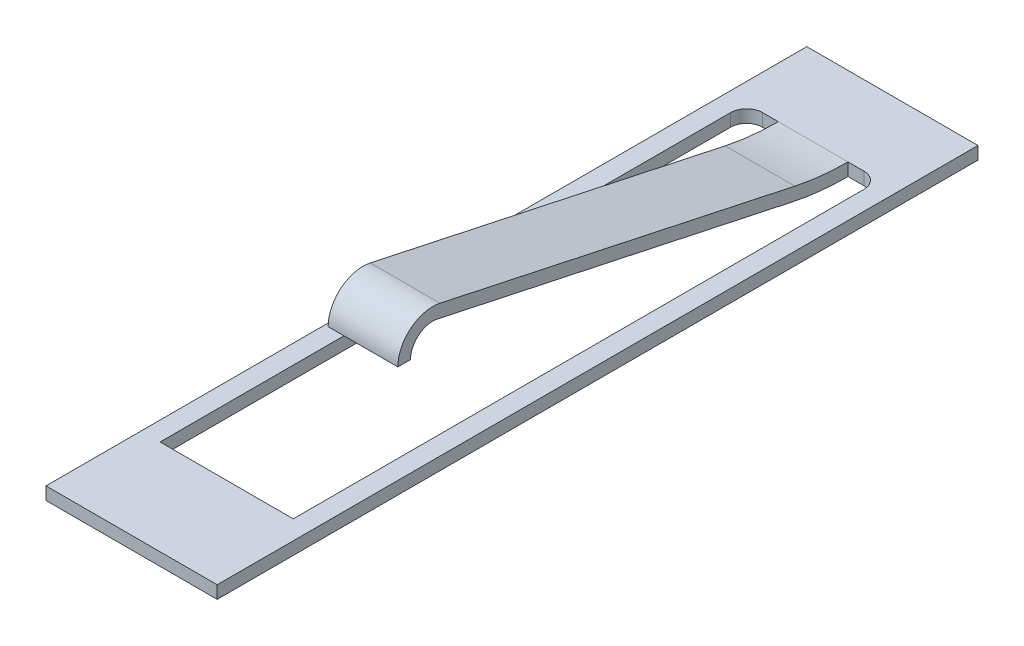
SolidWorks part; units mm, degrees
ref_plane "Front Plane" through (0, 0, 0) normal (0, 0, 1) x (1, 0, 0)
ref_plane "Top Plane" through (0, 0, 0) normal (0, 1, 0) x (1, 0, 0)
ref_plane "Right Plane" through (0, 0, 0) normal (1, 0, 0) x (0, 0, -1)
sketch "Sketch1" plane through (0, 0, 0) normal (0, 1, 0) x (1, 0, 0)
  line L0 (0, 6) -> (0, 0) construction
  line L1 (-1.35, 6) -> (1.35, 6)
  line L2 (-1.35, 6) -> (-1.35, -6)
  line L3 (-1.35, -6) -> (1.35, -6)
  line L4 (1.35, 6) -> (1.35, -6)
  line L5 (0, 0) -> (1.35, 0) construction
  line L6 (-0.55, 4.5) -> (-0.55, -2.35) construction
  line L7 (-0.55, -2.35) -> (0.55, -2.35) construction
  line L8 (0.55, -2.35) -> (0.55, 4.5) construction
  line L9 (-1.35, -1.8) -> (1.35, -1.8) construction
  line L10 (-0.8, 4.5) -> (-0.8, -6) construction
  line L11 (0.8, 4.5) -> (0.8, -6) construction
  line L12 (0.8, 4.5) -> (-0.8, 4.5) construction
  line L13 (1.05, 4.5) -> (1.05, -4.5) construction
  line L14 (1.05, -4.5) -> (-1.05, -4.5) construction
  line L15 (-1.05, -4.5) -> (-1.05, 4.5) construction
  line L16 (-0.55, -1.25) -> (0.55, -1.25) construction
  line L17 (0, -1.25) -> (0, -1.8) construction
  line L18 (0, -1.8) -> (0, -2.35) construction
  circle A0 centre (-0.8, 4.5) radius 0.25 construction
  circle A1 centre (0.8, 4.5) radius 0.25 construction
  dimension "D1" = 12
  dimension "D2" = 2.7
  dimension "D3" = 7.8
  dimension "D4" = 1.1
  dimension "D5" = 0.3
  dimension "D6" = 1.1
  dimension "D7" = 1.5
extrude "Boss-Extrude1" add sketch "Sketch1" along normal blind 0.2
sketch "Sketch2" plane through (0, 0, 0) normal (0, 1, 0) x (1, 0, 0)
  line L0 (-1.05, 4.5) -> (-1.05, -4.5)
  line L1 (-1.05, -4.5) -> (1.05, -4.5)
  line L2 (1.05, -4.5) -> (1.05, 4.5)
  line L3 (-0.8, 4.75) -> (0.8, 4.75)
  arc A0 (1.05, 4.5) -> (0.8, 4.75) centre (0.8, 4.5) ccw
  arc A2 (-1.05, 4.5) -> (-0.8, 4.75) centre (-0.8, 4.5) cw
  circle A3 centre (-0.8, 4.5) radius 0.25 construction
extrude "Cut-Extrude1" cut sketch "Sketch2" along normal through all
sketch "Sketch3" plane through (0, 0, 0) normal (1, 0, 0) x (0, 0, -1)
  line L0 (-1.8, 0) -> (-1.8, 0.95) construction
  line L1 (-2.35, 0) -> (-2.35, 0.95) construction
  line L2 (-2.35, 0.95) -> (-1.25, 0.95) construction
  line L3 (-2.35, 0) -> (-1.25, 0) construction
  line L4 (-1.8, 0.95) -> (-1.8, 1.5) construction
  line L5 (4.75, 0) -> (4.75, 0.2)
  line L6 (6, 0) -> (0, 0) construction
  line L7 (4.75, 0.2) -> (6, 0.2) construction
  line L8 (6, 0.2) -> (6, 0) construction
  line L9 (-1.6848, 1.4878) -> (3.9121, 0.2888)
  line L10 (-1.7267, 1.2922) -> (3.8702, 0.0932)
  line L11 (4.75, 0) -> (6, 0) construction
  line L12 (-2.15, 0.95) -> (-2.35, 0.95)
  circle A0 centre (-1.8, 0.95) radius 0.55 construction
  arc A1 (4.75, 0.2) -> (3.9121, 0.2888) centre (4.75, 4.2) cw
  arc A2 (4.75, 0) -> (3.8702, 0.0932) centre (4.75, 4.2) cw
  circle A3 centre (-1.8, 0.95) radius 0.35 construction
  arc A4 (-2.15, 0.95) -> (-1.7267, 1.2922) centre (-1.8, 0.95) cw
  arc A5 (-2.35, 0.95) -> (-1.6848, 1.4878) centre (-1.8, 0.95) cw
  dimension "D2" = 4
  dimension "D3" = 0.2
  dimension "D1" = 1.5
extrude "Boss-Extrude2" add sketch "Sketch3" along normal up to vertex (0.55 mm away) from vertex at -0.55 starting at point (-0.55, 0, 2.35)
sketch "Sketch4" plane through (0, 0, 0) normal (0, 1, 0) x (1, 0, 0)
  line L0 (-1.5, 0) -> (1.5, 0) construction
  line L1 (-1.5, 6.2) -> (1.5, 6.2)
  line L2 (-1.5, 6.2) -> (-1.5, -6.2) construction
  line L3 (-1.5, -6.2) -> (1.5, -6.2)
  line L4 (1.5, 6.2) -> (1.5, -6.2) construction
  line L5 (0, 0) -> (1.35, 0) construction
  line L6 (0, 0) -> (0, 6.2) construction
  line L7 (-1.5, -3.8) -> (1.5, -3.8)
  line L8 (-1.5, 3.8) -> (1.5, 3.8)
  line L9 (-1.5, 6.2) -> (-1.5, 3.8)
  line L10 (1.5, 3.8) -> (1.5, 6.2)
  line L11 (1.5, -3.8) -> (1.5, -6.2)
  line L12 (-1.5, -6.2) -> (-1.5, -3.8)
  dimension "D1" = 3
  dimension "D2" = 12.4
  dimension "D3" = 7.6
sketch "Sketch5" plane through (0, 0, 0) normal (1, 0, 0) x (0, 0, -1)
  line L0 (-1.5, 1.95) -> (-1.5, 0) construction
  line L1 (-1.5, 0) -> (4.75, 0) construction
  line L2 (4.75, 0) -> (6, 0) construction
  line L3 (6, 0) -> (6, 0.2) construction
  line L4 (6, 0.2) -> (4.75, 0.2) construction
  line L5 (4.75, 0.2) -> (4.75, 0) construction
  line L6 (-1.5, 1.95) -> (-1.5, 2.5) construction
  line L7 (-1.2813, 2.4546) -> (3.1592, 0.5299)
  circle A0 centre (-1.5, 1.95) radius 0.55
  circle A1 centre (-1.8, 0.95) radius 0.55 construction
  arc A2 (4.75, 0.2) -> (3.1592, 0.5299) centre (4.75, 4.2) cw
  arc A3 (3.9121, 0.2888) -> (4.75, 0.2) centre (4.75, 4.2) ccw construction
  dimension "D1" = 7.5
  dimension "D2" = 2.5
